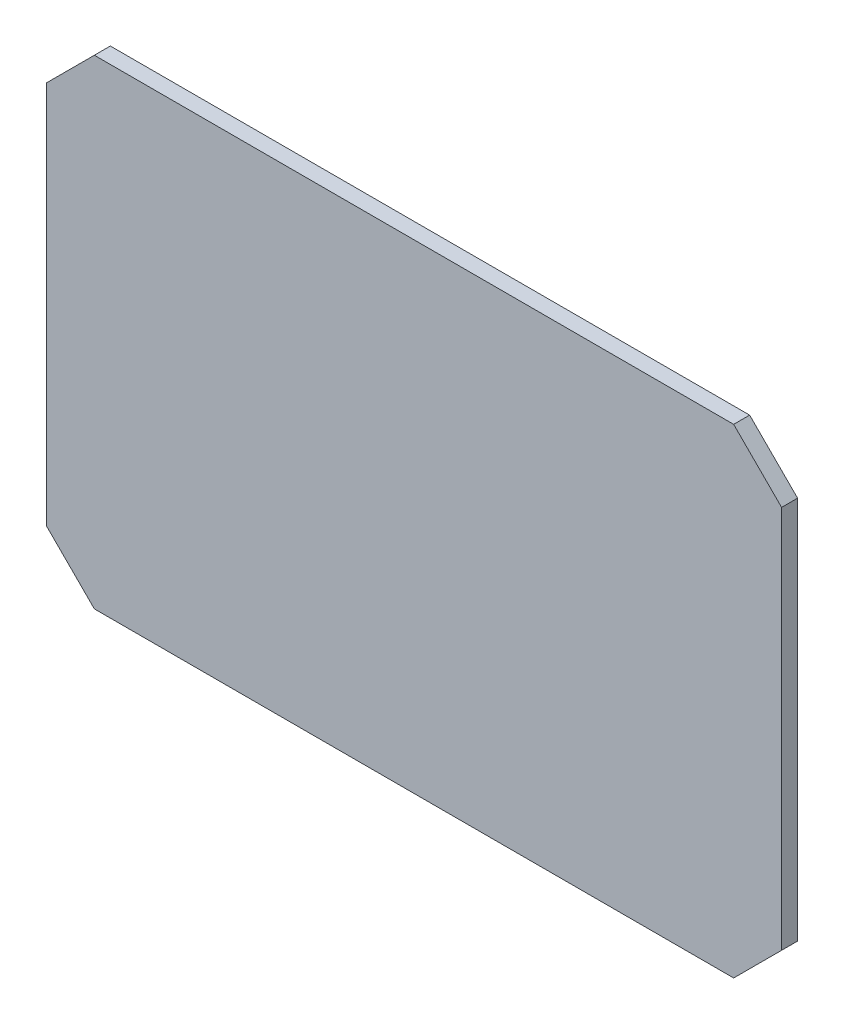
SolidWorks part; units mm, degrees
ref_plane "Front Plane" through (0, 0, 0) normal (0, 0, 1) x (1, 0, 0)
ref_plane "Top Plane" through (0, 0, 0) normal (0, 1, 0) x (1, 0, 0)
ref_plane "Right Plane" through (0, 0, 0) normal (1, 0, 0) x (0, 0, -1)
sketch "Sketch2" plane through (0, 0, 0) normal (0, 0, 1) x (1, 0, 0)
  line L0 (-230, 120) -> (-200, 150)
  line L1 (-200, 150) -> (200, 150)
  line L2 (-230, 120) -> (-230, -120)
  line L3 (-200, -150) -> (200, -150)
  line L4 (230, 120) -> (230, -120)
  line L5 (-230, 150) -> (230, -150) construction
  line L6 (-230, -150) -> (230, 150) construction
  line L7 (200, 150) -> (230, 120)
  line L8 (200, -150) -> (230, -120)
  line L9 (-230, -120) -> (-200, -150)
  point P0 (0, 0)
  dimension "D1" = 240
  dimension "D2" = 400
extrude "Boss-Extrude1" add sketch "Sketch2" along normal blind 10
